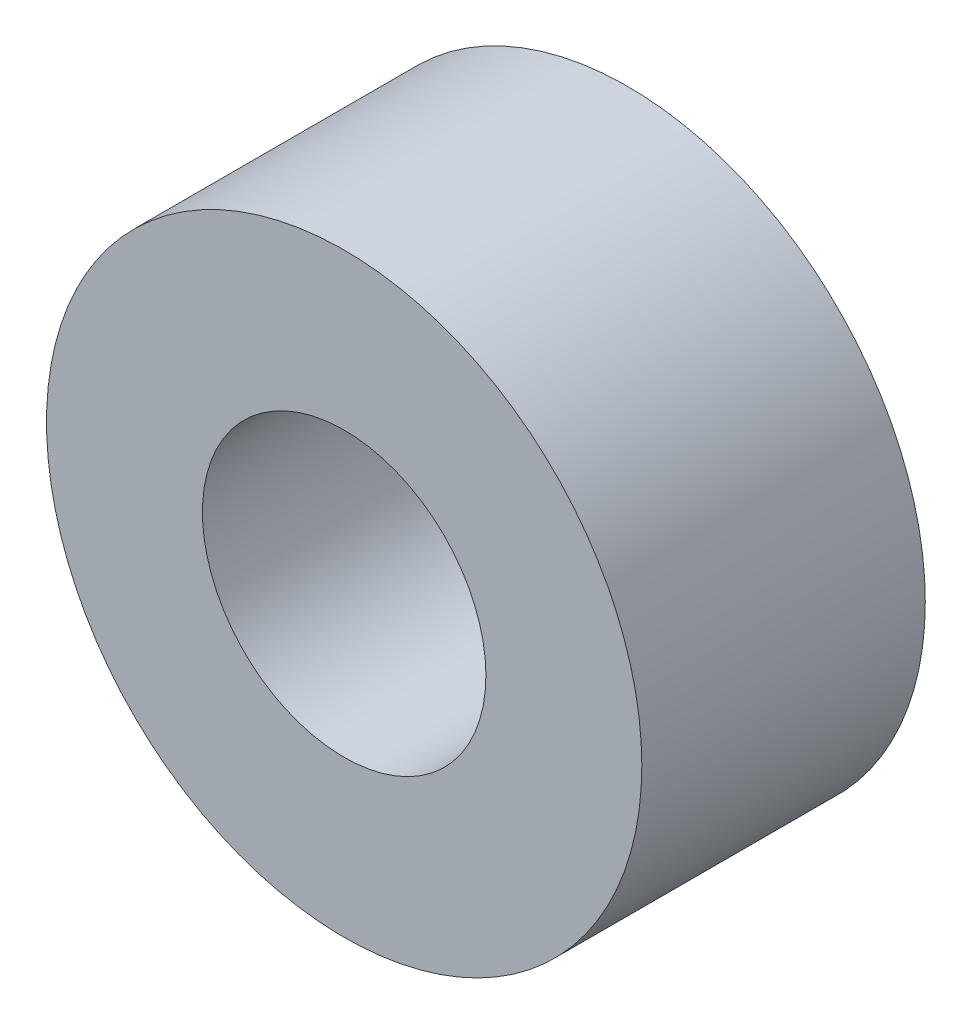
SolidWorks part; units mm, degrees
material "Stainless Steel (ferritic)"
ref_plane "Front Plane" through (0, 0, 0) normal (0, 0, 1) x (1, 0, 0)
ref_plane "Top Plane" through (0, 0, 0) normal (0, 1, 0) x (1, 0, 0)
ref_plane "Right Plane" through (0, 0, 0) normal (1, 0, 0) x (0, 0, -1)
sketch "Sketch1" plane through (0, 0, 0) normal (0, 0, 1) x (1, 0, 0)
  circle A0 centre (0, 0) radius 10.5
  circle A1 centre (0, 0) radius 5
  dimension "D1" = 21
  dimension "D2" = 10
extrude "Boss-Extrude1" add sketch "Sketch1" along normal blind 10
